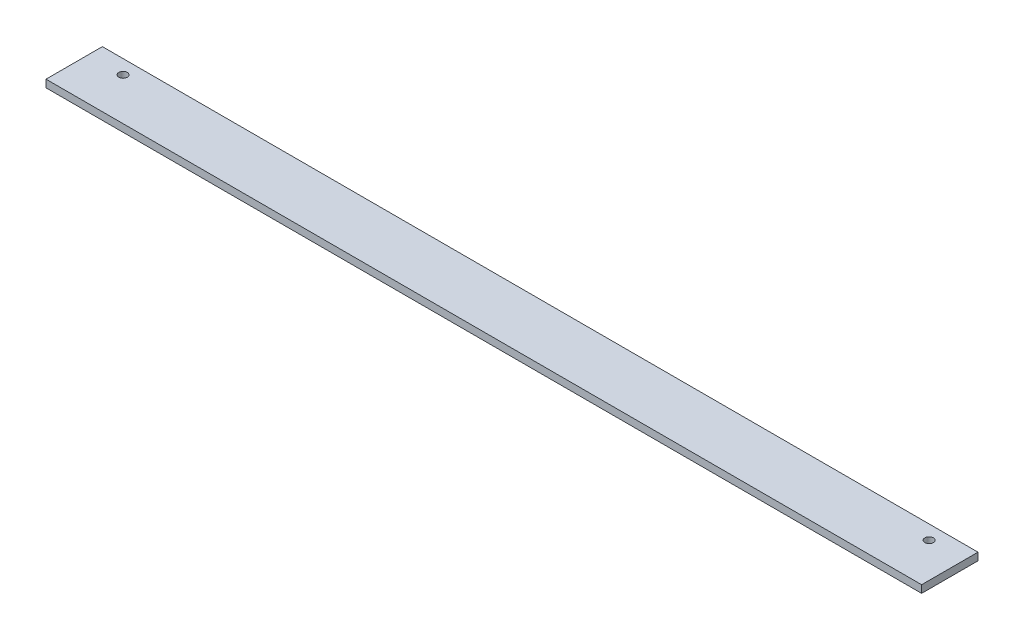
SolidWorks part; units mm, degrees
ref_plane "Спереди" through (0, 0, 0) normal (0, 0, 1) x (1, 0, 0)
ref_plane "Сверху" through (0, 0, 0) normal (0, 1, 0) x (1, 0, 0)
ref_plane "Справа" through (0, 0, 0) normal (1, 0, 0) x (0, 0, -1)
sketch "Эскиз1" plane through (0, 0, 0) normal (1, 0, 0) x (0, 0, -1)
  line L1 (-15, -2) -> (15, -2)
  line L2 (-15, -2) -> (-15, 2)
  line L3 (-15, 2) -> (15, 2)
  line L4 (15, -2) -> (15, 2)
  line L5 (-15, -2) -> (15, 2) construction
  line L6 (-15, 2) -> (15, -2) construction
  point P0 (0, 0)
  dimension "D1" = 4
  dimension "D2" = 30
extrude "Бобышка-Вытянуть1" add sketch "Эскиз1" along normal blind 466
sketch "Эскиз2" plane through (0, 2, 0) normal (0, 1, 0) x (1, 0, 0)
  line L0 (466, 15) -> (0, 15) construction
  line L1 (0, 15) -> (0, -15) construction
  line L2 (466, 15) -> (466, -15) construction
  circle A0 centre (18.5, 7.5) radius 2.25
  circle A1 centre (447.5, 7.5) radius 2.25
  dimension "D1" = 4.5
  dimension "D4" = 4.5
  dimension "D2" = 7.5
  dimension "D3" = 18.5
  dimension "D5" = 18.5
  dimension "D6" = 7.5
extrude "Вырез-Вытянуть1" cut sketch "Эскиз2" against normal through all
